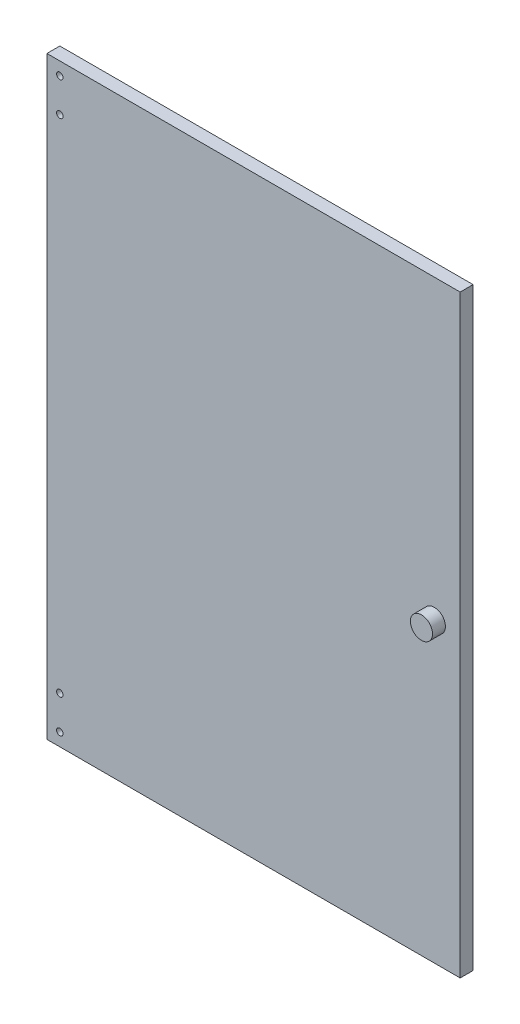
SolidWorks part; units mm, degrees
material "Glass"
ref_plane "Front Plane" through (0, 0, 0) normal (0, 0, 1) x (1, 0, 0)
ref_plane "Top Plane" through (0, 0, 0) normal (0, 1, 0) x (1, 0, 0)
ref_plane "Right Plane" through (0, 0, 0) normal (1, 0, 0) x (0, 0, -1)
sketch "Sketch1" plane through (0, 0, 0) normal (0, 0, 1) x (1, 0, 0)
  line L0 (-150, -230) -> (-150, 230) construction
  line L1 (-160, 230) -> (160, 230)
  line L2 (-160, 230) -> (-160, -230)
  line L3 (-160, -230) -> (160, -230)
  line L4 (160, 230) -> (160, -230)
  line L5 (-160, 230) -> (160, -230) construction
  line L6 (-160, -230) -> (160, 230) construction
  line L7 (0, -230) -> (0, 230) construction
  circle A0 centre (-150, -220) radius 2.5
  circle A2 centre (-150, 220) radius 2.5
  circle A4 centre (140, 0) radius 3
  circle A6 centre (-150, -194) radius 2.5
  circle A7 centre (-150, 194) radius 2.5
  point P0 (0, 0)
  dimension "D4" = 5
  dimension "D1" = 320
  dimension "D2" = 460
  dimension "D3" = 10
  dimension "D5" = 10
  dimension "D6" = 10
  dimension "D7" = 26
  dimension "D8" = 26
extrude "Boss-Extrude1" add sketch "Sketch1" along normal blind 10
sketch "Sketch2" plane through (0, 0, 10) normal (0, 0, 1) x (1, 0, 0)
  circle A0 centre (140, 0) radius 8.5784
extrude "Boss-Extrude2" add sketch "Sketch2" along normal blind 10
